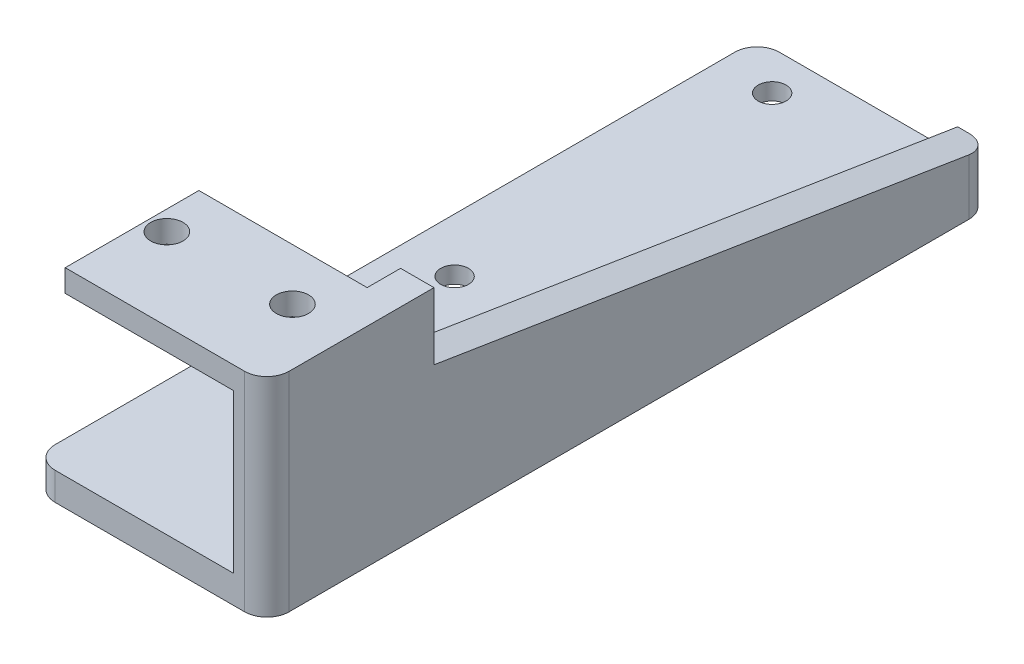
SolidWorks part; units mm, degrees
ref_plane "前视基准面" through (0, 0, 0) normal (0, 0, 1) x (1, 0, 0)
ref_plane "上视基准面" through (0, 0, 0) normal (0, 1, 0) x (1, 0, 0)
ref_plane "右视基准面" through (0, 0, 0) normal (1, 0, 0) x (0, 0, -1)
sketch "草图1" plane through (0, 0, 0) normal (0, 0, 1) x (1, 0, 0)
  line L0 (0, 2) -> (0, 0)
  line L1 (0, 0) -> (15.1, 0)
  line L2 (15.1, 0) -> (15.1, -14.2)
  line L4 (18.1, -16.7) -> (18.1, 2)
  line L5 (18.1, 2) -> (0, 2)
  line L6 (15.1, -14.2) -> (-2.9, -14.2)
  line L7 (-2.9, -14.2) -> (-2.9, -16.7)
  line L8 (-2.9, -16.7) -> (18.1, -16.7)
  point P5 (0, 0)
  point P9 (35.92, 3.2795)
  dimension "D1" = 14.2
  dimension "D2" = 15.1
  dimension "D3" = 2
  dimension "D4" = 3
  dimension "D5" = 18
  dimension "D6" = 2.5
extrude "凸台-拉伸1" add sketch "草图1" along normal blind 65
sketch "草图2" plane through (0, 2, 0) normal (0, 1, 0) x (1, 0, 0)
  line L0 (15.1, -65) -> (15.1, 0) construction
  line L1 (0, 0) -> (15.1, 0)
  line L2 (0, 0) -> (0, -53)
  line L3 (0, -53) -> (15.1, -53)
  line L4 (15.1, 0) -> (15.1, -53)
  line L5 (18.1, -65) -> (0, -65) construction
  line L6 (1.765, -57.64) -> (13.035, -57.64) construction
  line L7 (7.55, -53) -> (7.55, -47.5465) construction
  circle A0 centre (1.765, -57.64) radius 1.45
  circle A1 centre (13.035, -57.64) radius 1.45
  point P13 (7.4, -57.64)
  dimension "D2" = 2.9
  dimension "D1" = 12
  dimension "D3" = 11.27
  dimension "D4" = 0.15
  dimension "D5" = 7.36
extrude "切除-拉伸1" cut sketch "草图2" against normal up to next
sketch "草图3" plane through (0, -14.2, 0) normal (0, 1, 0) x (1, 0, 0)
  line L0 (1.95, -3.5) -> (1.95, -32) construction
  line L1 (15.1, -65) -> (15.1, 0) construction
  line L2 (18.1, -65) -> (0, -65) construction
  circle A0 centre (1.95, -3.5) radius 1.25
  circle A1 centre (1.95, -32) radius 1.25
  dimension "D1" = 2.5
  dimension "D2" = 28.5
  dimension "D3" = 13.15
  dimension "D4" = 33
extrude "切除-拉伸2" cut sketch "草图3" against normal up to next
sketch "草图4" plane through (18.1, 0, 0) normal (1, 0, 0) x (0, 0, -1)
  line L0 (-50, 2) -> (0, 2)
  line L1 (-65, 2) -> (0, 2) construction
  line L2 (0, 2) -> (0, -12)
  line L3 (0, -16.7) -> (0, 2) construction
  line L4 (0, -12) -> (-50, -4)
  line L5 (-50, -4) -> (-50, 2)
  dimension "D1" = 50
  dimension "D2" = 6
  dimension "D3" = 14
extrude "切除-拉伸3" cut sketch "草图4" against normal up to next
fillet "圆角1" radius 2 4 edges at (18.1, -7.35, 65) (-2.9, -15.45, 65) (18.1, -14.35, 0) (-2.9, -15.45, 0)
sketch "草图5" plane through (0, -16.7, 0) normal (0, -1, 0) x (1, 0, 0)
  circle A0 centre (1.95, 32) radius 2.7
  circle A1 centre (1.95, 3.5) radius 2.7
  dimension "D1" = 5.4
extrude "切除-拉伸4" cut sketch "草图5" against normal blind 1
